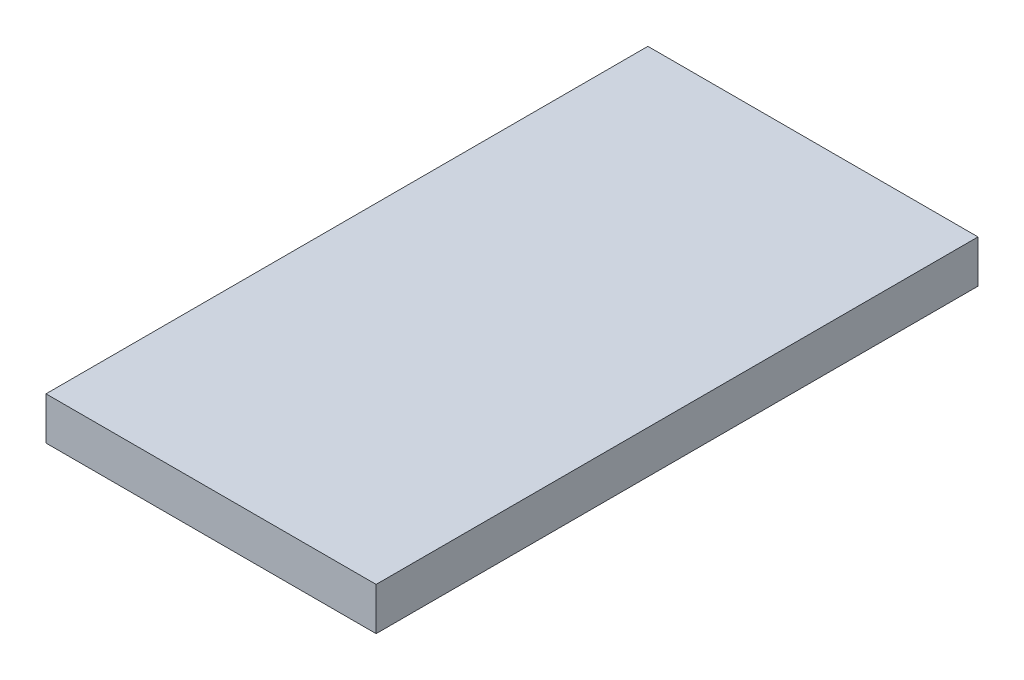
SolidWorks part; units mm, degrees
ref_plane "Front" through (0, 0, 0) normal (0, 0, 1) x (1, 0, 0)
ref_plane "Top" through (0, 0, 0) normal (0, 1, 0) x (1, 0, 0)
ref_plane "Right" through (0, 0, 0) normal (1, 0, 0) x (0, 0, -1)
sketch "Sketch1" plane through (0, 0, 0) normal (0, 1, 0) x (1, 0, 0)
  line L1 (0, 0) -> (23.2, 0)
  line L2 (0, 0) -> (0, -42.3)
  line L3 (0, -42.3) -> (23.2, -42.3)
  line L4 (23.2, 0) -> (23.2, -42.3)
  dimension "D1" = 23.2
  dimension "D2" = 42.3
extrude "Boss-Extrude1" add sketch "Sketch1" along normal blind 3
